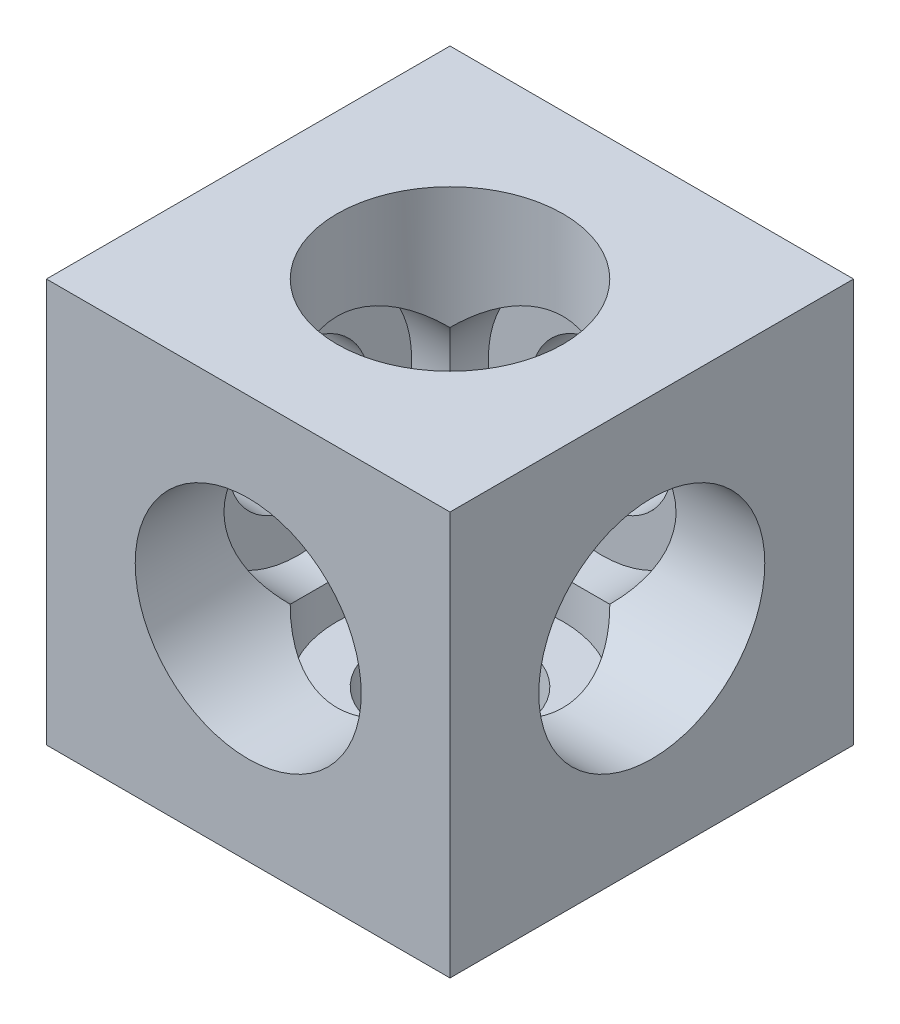
SolidWorks part; units mm, degrees
material "6061-T6 (SS)"
ref_plane "Front Plane" through (0, 0, 0) normal (0, 0, 1) x (1, 0, 0)
ref_plane "Top Plane" through (0, 0, 0) normal (0, 1, 0) x (1, 0, 0)
ref_plane "Right Plane" through (0, 0, 0) normal (1, 0, 0) x (0, 0, -1)
sketch "Sketch1" plane through (0, 0, 0) normal (0, 0, 1) x (1, 0, 0)
  line L1 (10, -10) -> (-10, -10)
  line L2 (10, -10) -> (10, 10)
  line L3 (10, 10) -> (-10, 10)
  line L4 (-10, -10) -> (-10, 10)
  line L5 (10, -10) -> (-10, 10) construction
  line L6 (10, 10) -> (-10, -10) construction
  point P0 (0, 0)
  dimension "D1" = 20
extrude "Boss-Extrude1" add sketch "Sketch1" along normal mid plane 20
sketch "Sketch2" plane through (0, 10, 0) normal (0, 1, 0) x (1, 0, 0)
  circle A0 centre (0, 0) radius 3.5
  dimension "D1" = 7
extrude "Cut-Extrude1" cut sketch "Sketch2" against normal through all
sketch "Sketch3" plane through (0, 0, 10) normal (0, 0, 1) x (1, 0, 0)
  circle A0 centre (0, 0) radius 3.5
  dimension "D1" = 7
extrude "Cut-Extrude2" cut sketch "Sketch3" against normal through all
sketch "Sketch4" plane through (10, 0, 0) normal (1, 0, 0) x (0, 0, -1)
  circle A0 centre (0, 0) radius 3.5
  dimension "D1" = 7
extrude "Cut-Extrude3" cut sketch "Sketch4" against normal through all
sketch "Sketch5" plane through (0, 10, 0) normal (0, 1, 0) x (1, 0, 0)
  circle A0 centre (0, 0) radius 5.6
  dimension "D1" = 11.2
extrude "Cut-Extrude4" cut sketch "Sketch5" against normal blind 17.5
sketch "Sketch6" plane through (0, 0, 10) normal (0, 0, 1) x (1, 0, 0)
  circle A0 centre (0, 0) radius 5.6
  dimension "D1" = 11.2
extrude "Cut-Extrude5" cut sketch "Sketch6" against normal blind 17.5
sketch "Sketch7" plane through (10, 0, 0) normal (1, 0, 0) x (0, 0, -1)
  circle A0 centre (0, 0) radius 5.6
  dimension "D1" = 11.2
extrude "Cut-Extrude6" cut sketch "Sketch7" against normal blind 17.5
